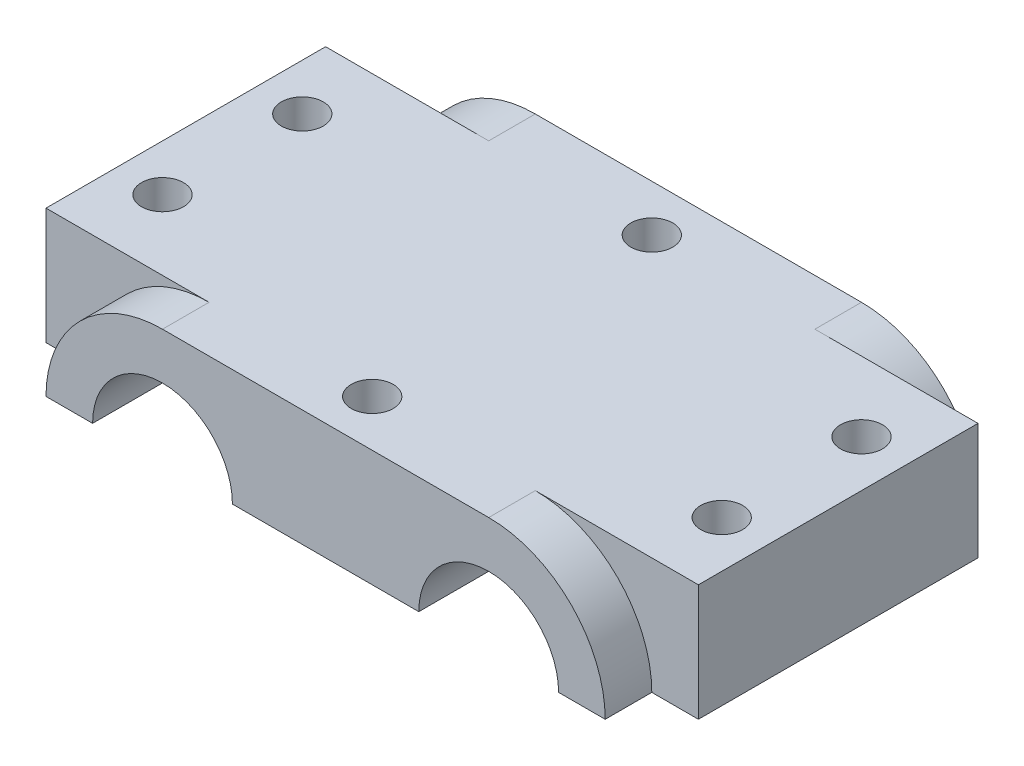
SolidWorks part; units mm, degrees
ref_plane "Front Plane" through (0, 0, 0) normal (0, 0, 1) x (1, 0, 0)
ref_plane "Top Plane" through (0, 0, 0) normal (0, 1, 0) x (1, 0, 0)
ref_plane "Right Plane" through (0, 0, 0) normal (1, 0, 0) x (0, 0, -1)
sketch "Sketch1" plane through (0, 0, 0) normal (0, 1, 0) x (1, 0, 0)
  line L1 (-35, -15) -> (35, -15)
  line L2 (-35, -15) -> (-35, 15)
  line L3 (-35, 15) -> (35, 15)
  line L4 (35, -15) -> (35, 15)
  point P0 (0, 0)
extrude "Boss-Extrude1" add sketch "Sketch1" along normal mid plane 12.5
sketch "Sketch2" plane through (0, 0, 15) normal (0, 0, 1) x (1, 0, 0)
  line L0 (10, -6.25) -> (-10, -6.25)
  line L1 (-35, -6.25) -> (35, -6.25) construction
  line L2 (-17.5, 6.25) -> (17.5, 6.25)
  line L3 (-5, -6.25) -> (5, -6.25)
  line L5 (-10, -6.25) -> (10, -6.25)
  line L6 (-25, -6.25) -> (-30, -6.25)
  line L7 (5, -6.25) -> (10, -6.25)
  line L8 (25, -6.25) -> (30, -6.25)
  arc A0 (25, -6.25) -> (10, -6.25) centre (17.5, -6.25) ccw
  arc A1 (30, -6.25) -> (17.5, 6.25) centre (17.5, -6.25) ccw
  arc A2 (-10, -6.25) -> (-25, -6.25) centre (-17.5, -6.25) ccw
  arc A3 (-17.5, 6.25) -> (-30, -6.25) centre (-17.5, -6.25) ccw
  line M1 (-35, -6.25) -> (35, -6.25)
  line M3 (35, 6.25) -> (-35, 6.25)
extrude "Boss-Extrude2" add sketch "Sketch2" along normal blind 5 and the other way blind 35 contours A3 A2 L0 A0 A1 M3 M1
sketch "Sketch4" plane through (0, 0, 20) normal (0, 0, 1) x (1, 0, 0)
  line L0 (-25, -6.25) -> (-10, -6.25) construction
  line L1 (10, -6.25) -> (25, -6.25) construction
  line L2 (-25, -6.25) -> (-10, -6.25)
  line L3 (10, -6.25) -> (25, -6.25)
  arc A0 (-10, -6.25) -> (-25, -6.25) centre (-17.5, -6.25) ccw construction
  arc A1 (25, -6.25) -> (10, -6.25) centre (17.5, -6.25) ccw construction
  arc A2 (-10, -6.25) -> (-25, -6.25) centre (-17.5, -6.25) ccw
  arc A3 (25, -6.25) -> (10, -6.25) centre (17.5, -6.25) ccw
extrude "Cut-Extrude1" cut sketch "Sketch4" against normal blind 40
sketch "Sketch5" plane through (0, 6.25, 0) normal (0, 1, 0) x (1, 0, 0)
  circle A0 centre (-30, 7.5) radius 2.25
  circle A1 centre (-30, -7.5) radius 2.25
  circle A2 centre (30, -7.5) radius 2.25
  circle A3 centre (30, 7.5) radius 2.25
  circle A4 centre (0, 15) radius 2.25
  circle A5 centre (0, -15) radius 2.25
  point P4 (0, 0)
  point P8 (-30, 0)
extrude "Cut-Extrude2" cut sketch "Sketch5" against normal blind 12.5
